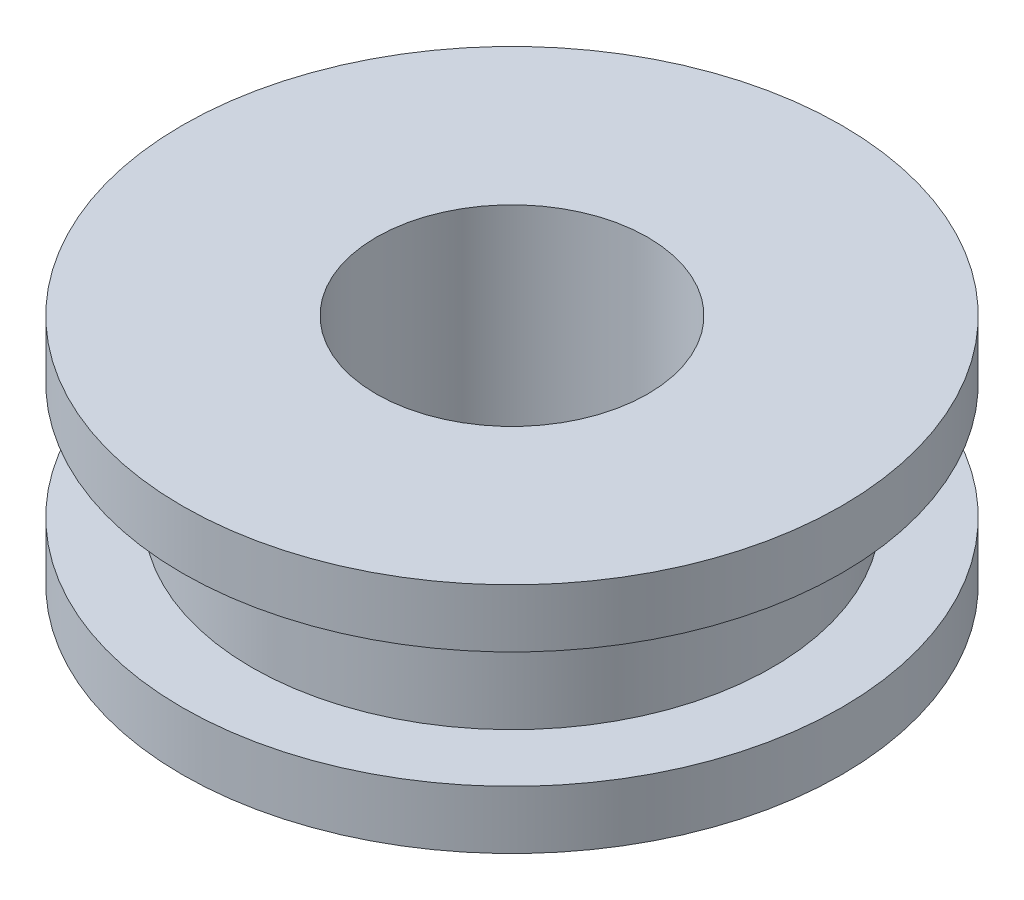
SolidWorks part; units mm, degrees
ref_plane "Vorne" through (0, 0, 0) normal (0, 0, 1) x (1, 0, 0)
ref_plane "Oben" through (0, 0, 0) normal (0, 1, 0) x (1, 0, 0)
ref_plane "Rechts" through (0, 0, 0) normal (1, 0, 0) x (0, 0, -1)
sketch "Skizze1" plane through (0, 0, 0) normal (0, 1, 0) x (1, 0, 0)
  circle A0 centre (0, 0) radius 8.5
  circle A1 centre (0, 0) radius 3.5
  dimension "D1" = 7
  dimension "D2" = 17
extrude "Aufsatz-Linear austragen1" add sketch "Skizze1" along normal blind 6
sketch "Skizze2" plane through (0, 0, 0) normal (0, 1, 0) x (1, 0, 0)
  circle A0 centre (0, 0) radius 6.7097
  circle A1 centre (0, 0) radius 13.8901
extrude "Schnitt-Linear austragen1" cut sketch "Skizze2" along normal blind 3 from offset 1.5
